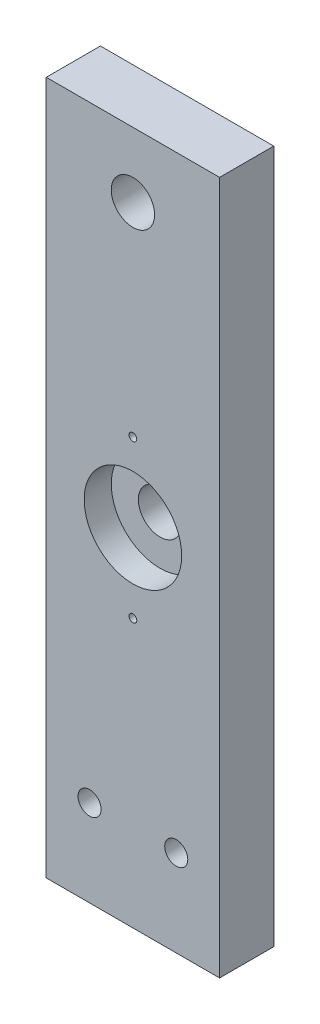
SolidWorks part; units mm, degrees
ref_plane "Front Plane" through (0, 0, 0) normal (0, 0, 1) x (1, 0, 0)
ref_plane "Top Plane" through (0, 0, 0) normal (0, 1, 0) x (1, 0, 0)
ref_plane "Right Plane" through (0, 0, 0) normal (1, 0, 0) x (0, 0, -1)
sketch "Sketch1" plane through (0, 0, 0) normal (0, 0, 1) x (1, 0, 0)
  line L0 (25.4, 177.8) -> (-25.4, 177.8) construction
  line L1 (-25.4, -25.4) -> (25.4, -25.4)
  line L2 (-25.4, -25.4) -> (-25.4, 177.8)
  line L3 (-25.4, 177.8) -> (25.4, 177.8)
  line L4 (25.4, -25.4) -> (25.4, 177.8)
  line L5 (25.4, 25.4) -> (25.4, -25.4) construction
extrude "Boss-Extrude1" add sketch "Sketch1" along normal blind 15.875 contours L4 L3 L2 L1
sketch "Sketch2" plane through (0, 0, 15.875) normal (0, 0, 1) x (1, 0, 0)
  circle A0 centre (-12.7, 0) radius 3.3782 construction
  circle A1 centre (12.7, 0) radius 3.3782 construction
  circle A2 centre (-12.7, 0) radius 3.3782
  circle A3 centre (12.7, 0) radius 3.3782
hole_wizard "1/4 Clearance Hole1" positions "Sketch3" profile "Sketch4" hole size "1/4" standard "ANSI Inch" end condition through all
sketch "Sketch3" plane through (0, 0, 15.875) normal (0, 0, 1) x (1, 0, 0)
  point P0 (12.7, 0)
  point P3 (-12.7, 0)
sketch "Sketch4" plane through (12.7, 0, 15.875) normal (1, 0, 0) x (0, -1, 0)
  line L0 (0, 0) -> (0, 15.875)
  line L1 (0, 15.875) -> (3.3782, 15.875)
  line L2 (3.3782, 15.875) -> (3.3782, 0)
  line L5 (3.3782, 0) -> (0, 0)
  line L11 (0, -6.35) -> (0, 107.95) construction
  dimension "Thru Hole Dia." = 6.7564
  dimension "Thru Hole Depth" = 15.875
sketch "Sketch5" plane through (0, 0, 0) normal (0, 0, -1) x (-1, 0, 0)
  circle A0 centre (0, 158.75) radius 6.35 construction
  circle A1 centre (0, 158.75) radius 6.35
  circle A2 centre (0, 76.2) radius 6.35 construction
  circle A3 centre (0, 76.2) radius 6.35
extrude "Cut-Extrude1" cut sketch "Sketch5" against normal through all
sketch "Sketch6" plane through (0, 0, 15.875) normal (0, 0, 1) x (1, 0, 0)
  circle A0 centre (0, 76.2) radius 14.2875 construction
  circle A1 centre (0, 76.2) radius 14.2875
extrude "Cut-Extrude2" cut sketch "Sketch6" against normal blind 7.9375 contours A1
sketch "Sketch7" plane through (0, 0, 15.875) normal (0, 0, 1) x (1, 0, 0)
  line L0 (0, 53.213) -> (0, 99.187)
  circle A0 centre (0, 76.2) radius 14.2875 construction
  point P5 (0, 76.2)
  dimension "D1" = 45.974
hole_wizard "#4-40 Tapped Hole1" positions "Sketch8" profile "Sketch9" tap size "#4-40" standard "ANSI Inch"
sketch "Sketch8" plane through (0, 0, 15.875) normal (0, 0, 1) x (1, 0, 0)
  point P0 (0, 99.187)
  point P3 (0, 53.213)
sketch "Sketch9" plane through (0, 99.187, 15.875) normal (1, 0, 0) x (0, -1, 0)
  line L0 (0, 0) -> (0, 8.2992)
  line L1 (0, 8.2992) -> (1.1303, 7.62)
  line L2 (1.1303, 7.62) -> (1.1303, 0)
  line L5 (1.1303, 0) -> (0, 0)
  line L10 (0, 8.2992) -> (-1.1303, 7.62) construction
  line L11 (0, -6.35) -> (0, 107.95) construction
  dimension "Tap Drill Dia." = 2.2606
  dimension "Tap Drill Depth" = 7.62
  dimension "Drill Angle" = 118
cosmetic thread "Hole Thread1" parameters "D1"=5.588, "D2"=2.8448
cosmetic thread "Hole Thread2" parameters "D1"=5.588, "D2"=2.8448
hole_wizard "1/4-20 Tapped Hole1" [suppressed] positions "Sketch10" profile "Sketch11" tap size "1/4-20" standard "ANSI Inch"
sketch "Sketch10" plane through (-25.4, 0, 0) normal (-1, 0, 0) x (0, 0, 1)
  line L0 (15.875, 177.8) -> (0, 177.8) construction
  point P0 (7.9375, 139.7)
  point P2 (7.9375, 107.95)
  point P8 (7.9375, 177.8)
  dimension "D1" = 38.1
  dimension "D2" = 31.75
sketch "Sketch11" plane through (-25.4, 139.7, 7.9375) normal (0, 1, 0) x (0, 0, 1)
  line L0 (0, 0) -> (0, 18.0438)
  line L1 (0, 18.0438) -> (2.5527, 16.51)
  line L2 (2.5527, 16.51) -> (2.5527, 0)
  line L5 (2.5527, 0) -> (0, 0)
  line L10 (0, 18.0438) -> (-2.5527, 16.51) construction
  line L11 (0, -6.35) -> (0, 107.95) construction
  dimension "Tap Drill Dia." = 5.1054
  dimension "Tap Drill Depth" = 16.51
  dimension "Drill Angle" = 118
cosmetic thread "Hole Thread3" [suppressed] parameters "D1"=12.7, "D2"=6.35
cosmetic thread "Hole Thread4" [suppressed] parameters "D1"=12.7, "D2"=6.35
equation "\"UprightThickness\"=0.625"
equation "\"D1@Boss-Extrude1\"=\"UprightThickness\""
